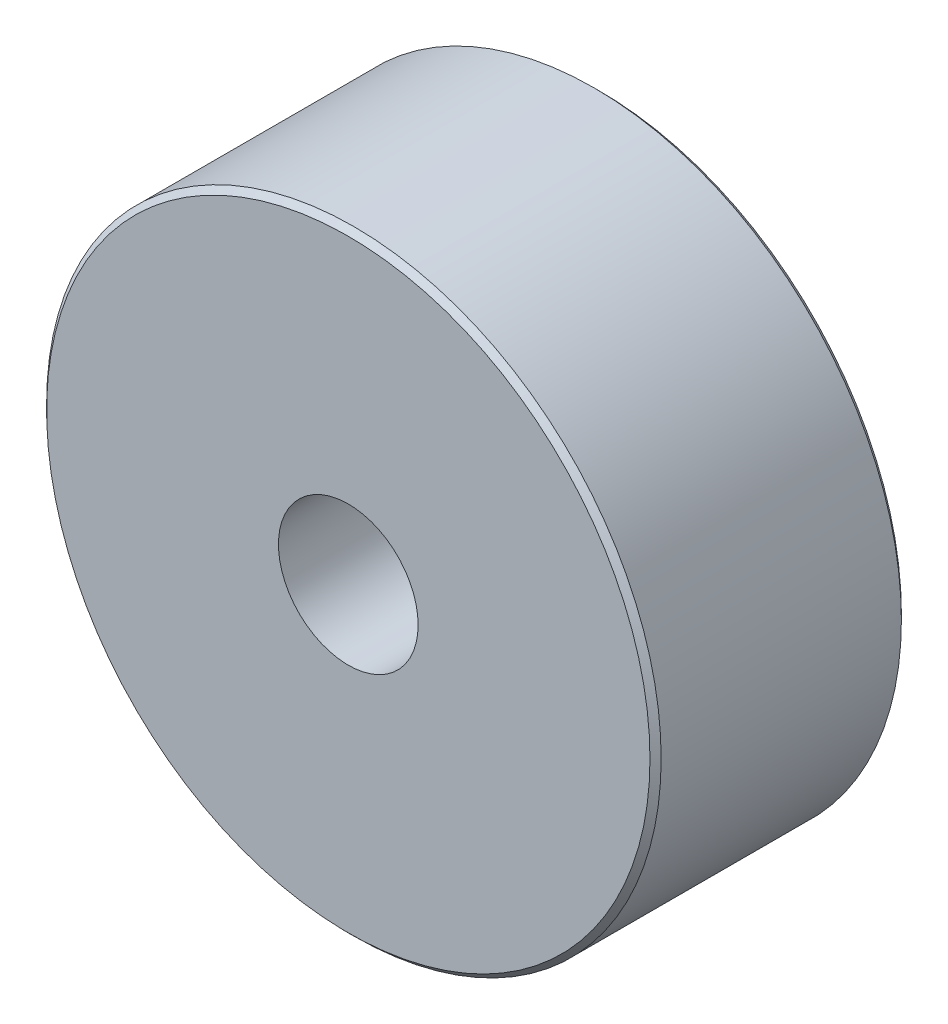
SolidWorks part; units mm, degrees
material "XC38"
ref_plane "Face" through (0, 0, 0) normal (0, 0, 1) x (1, 0, 0)
ref_plane "Dessus" through (0, 0, 0) normal (0, 1, 0) x (1, 0, 0)
ref_plane "Droite" through (0, 0, 0) normal (1, 0, 0) x (0, 0, -1)
sketch "Esquisse1" plane through (0, 0, 0) normal (0, 0, 1) x (1, 0, 0)
  circle A0 centre (0, 0) radius 5.5
  dimension "D1" = 11
extrude "Boss.-Extru.1" add sketch "Esquisse1" along normal blind 4.5
hole_wizard "Trou taraudé M31" positions "Esquisse3" profile "Esquisse4" tap size "M3" standard "ISO" end condition through all
sketch "Esquisse3" plane through (0, 0, 4.5) normal (0, 0, 1) x (1, 0, 0)
  point P0 (0, 0)
sketch "Esquisse4" plane through (0, 0, 4.5) normal (1, 0, 0) x (0, -1, 0)
  line L0 (0, 0) -> (0, 4.5)
  line L1 (0, 4.5) -> (1.25, 4.5)
  line L2 (1.25, 4.5) -> (1.25, 0)
  line L5 (1.25, 0) -> (0, 0)
  line L11 (0, -6.35) -> (0, 107.95) construction
  dimension "Diamètre du trou pour taraudage jusqu'au prochain" = 2.5
  dimension "Profondeur du trou pour taraudage jusqu'au prochain" = 4.5
cosmetic thread "Filetage de perçage1" parameters "D2"=3
chamfer "Chanfrein1" distance 0.1 angle 45 2 edges at (5.5, 0, 0) (5.5, 0, 4.5)
